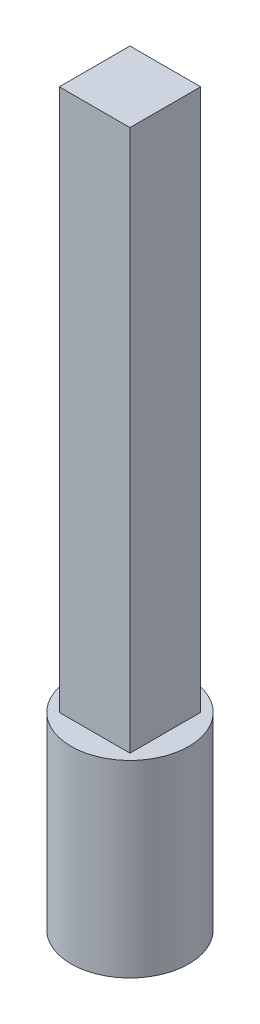
SolidWorks part; units mm, degrees
ref_plane "前视基准面" through (0, 0, 0) normal (0, 0, 1) x (1, 0, 0)
ref_plane "上视基准面" through (0, 0, 0) normal (0, 1, 0) x (1, 0, 0)
ref_plane "右视基准面" through (0, 0, 0) normal (1, 0, 0) x (0, 0, -1)
sketch "草图1" plane through (0, 0, 0) normal (0, 1, 0) x (1, 0, 0)
  circle A0 centre (0, 0) radius 25
  dimension "D1" = 50
extrude "凸台-拉伸1" add sketch "草图1" along normal blind 80
sketch "草图2" plane through (0, 80, 0) normal (0, 1, 0) x (1, 0, 0)
  line L1 (-15, 15) -> (15, 15)
  line L2 (-15, 15) -> (-15, -15)
  line L3 (-15, -15) -> (15, -15)
  line L4 (15, 15) -> (15, -15)
  line L5 (-15, 15) -> (15, -15) construction
  line L6 (-15, -15) -> (15, 15) construction
  point P0 (0, 0)
  dimension "D1" = 30
  dimension "30" = 30
extrude "凸台-拉伸2" add sketch "草图2" along normal blind 230
sketch "草图3" plane through (0, 0, 0) normal (1, 0, 0) x (0, 0, -1)
  line L0 (0, 0) -> (-25, 0)
  line L1 (-25, 0) -> (0, -31.9048)
  line L2 (0, -31.9048) -> (0, 0)
revolve "旋转1" [suppressed] add sketch "草图3" angle 360 about L2
